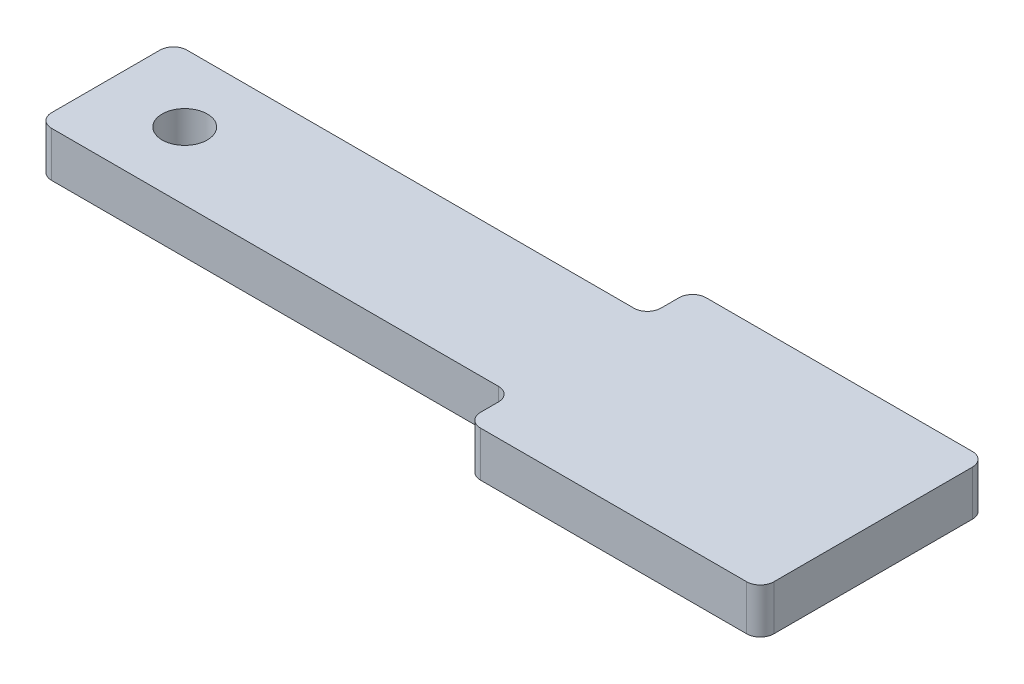
SolidWorks part; units mm, degrees
material "Copper"
ref_plane "Front Plane" through (0, 0, 0) normal (0, 0, 1) x (1, 0, 0)
ref_plane "Top Plane" through (0, 0, 0) normal (0, 1, 0) x (1, 0, 0)
ref_plane "Right Plane" through (0, 0, 0) normal (1, 0, 0) x (0, 0, -1)
sketch "Sketch1" plane through (0, 0, 0) normal (0, 1, 0) x (1, 0, 0)
  line L0 (-15, 1.5) -> (0, 1.5) construction
  line L1 (-4.5, 0) -> (-15, 0)
  line L2 (2, -1) -> (2, 4)
  line L3 (-4.5, 3) -> (-15, 3)
  line L4 (-15, 0) -> (-15, 3)
  line L5 (-4.5, 0) -> (-4.5, -1)
  line L6 (-4.5, 3) -> (-4.5, 4)
  line L7 (-4.5, 4) -> (2, 4)
  line L8 (-4.5, -1) -> (2, -1)
  circle A0 centre (-13.25, 1.5) radius 0.5
  dimension "D3" = 1
  dimension "D4" = 1.5
  dimension "D5" = 1.75
  dimension "D1" = 17
  dimension "D2" = 3
  dimension "D6" = 1
  dimension "D7" = 6.5
extrude "Boss-Extrude1" add sketch "Sketch1" along normal blind 1
fillet "Fillet1" radius 0.3 8 edges at (-15, 0.5, -3) (-4.5, 0.5, -3) (-4.5, 0.5, -4) (2, 0.5, -4) (2, 0.5, 1) (-4.5, 0.5, 1) (-4.5, 0.5, 0) (-15, 0.5, 0)
equation "\"D4@Sketch1\"=\"D2@Sketch1\"/2"
